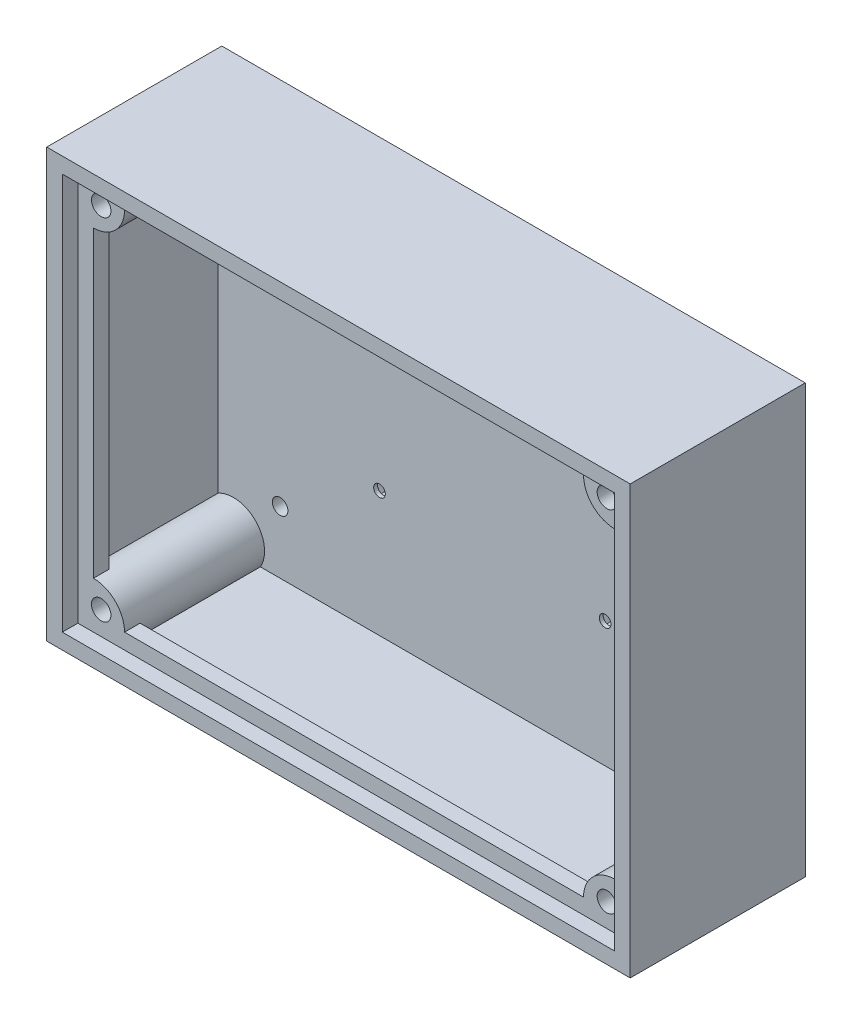
SolidWorks part; units mm, degrees
ref_plane "Front Plane" through (0, 0, 0) normal (0, 0, 1) x (1, 0, 0)
ref_plane "Top Plane" through (0, 0, 0) normal (0, 1, 0) x (1, 0, 0)
ref_plane "Right Plane" through (0, 0, 0) normal (1, 0, 0) x (0, 0, -1)
sketch "Sketch1" plane through (0, 0, 0) normal (0, 0, 1) x (1, 0, 0)
  line L1 (-102.1814, 48.3946) -> (47.8186, 48.3946)
  line L2 (-102.1814, 48.3946) -> (-102.1814, -61.6054)
  line L3 (-102.1814, -61.6054) -> (47.8186, -61.6054)
  line L4 (47.8186, 48.3946) -> (47.8186, -61.6054)
  dimension "D1" = 110
  dimension "D2" = 150
extrude "Boss-Extrude1" add sketch "Sketch1" along normal blind 5
sketch "Sketch2" plane through (0, 0, 5) normal (0, 0, 1) x (-1, 0, 0)
  line L0 (56.6312, -23.6539) -> (-1.3688, -23.6539) construction
  line L1 (-1.3688, -23.6539) -> (-1.3688, 25.3461) construction
  line L2 (-1.3688, 25.3461) -> (56.6312, 25.3461) construction
  line L3 (56.6312, 25.3461) -> (56.6312, -23.6539) construction
  line L4 (73.9008, -28.3946) -> (73.9008, 31.3544) construction
  line L5 (73.9008, 31.3544) -> (-19.5381, 31.3544) construction
  line L6 (-19.5381, 31.3544) -> (-19.5381, -28.3946) construction
  line L7 (-19.5381, -28.3946) -> (73.9008, -28.3946) construction
  line L8 (102.1814, 61.6054) -> (-47.8186, 61.6054) construction
  line L9 (0.9983, 25.3461) -> (-0.1852, 27.3961)
  line L10 (-47.8186, 61.6054) -> (-47.8186, -48.3946) construction
  line L11 (-47.8186, -48.3946) -> (102.1814, -48.3946) construction
  line L12 (-0.1852, 27.3961) -> (-2.5524, 27.3961)
  line L13 (-2.5524, 27.3961) -> (-3.7359, 25.3461)
  line L14 (-3.7359, 25.3461) -> (-2.5524, 23.2961)
  line L15 (-2.5524, 23.2961) -> (-0.1852, 23.2961)
  line L16 (-0.1852, 23.2961) -> (0.9983, 25.3461)
  line L17 (55.4476, 27.3961) -> (54.2641, 25.3461)
  line L18 (54.2641, 25.3461) -> (55.4476, 23.2961)
  line L19 (55.4476, 23.2961) -> (57.8148, 23.2961)
  line L20 (57.8148, 23.2961) -> (58.9983, 25.3461)
  line L21 (58.9983, 25.3461) -> (57.8148, 27.3961)
  line L22 (57.8148, 27.3961) -> (55.4476, 27.3961)
  line L23 (-0.1852, -21.6039) -> (-2.5524, -21.6039)
  line L24 (-2.5524, -21.6039) -> (-3.7359, -23.6539)
  line L25 (-3.7359, -23.6539) -> (-2.5524, -25.7039)
  line L26 (-2.5524, -25.7039) -> (-0.1852, -25.7039)
  line L27 (-0.1852, -25.7039) -> (0.9983, -23.6539)
  line L28 (0.9983, -23.6539) -> (-0.1852, -21.6039)
  line L29 (55.4476, -21.6039) -> (54.2641, -23.6539)
  line L30 (54.2641, -23.6539) -> (55.4476, -25.7039)
  line L31 (55.4476, -25.7039) -> (57.8148, -25.7039)
  line L32 (57.8148, -25.7039) -> (58.9983, -23.6539)
  line L33 (58.9983, -23.6539) -> (57.8148, -21.6039)
  line L34 (57.8148, -21.6039) -> (55.4476, -21.6039)
  circle A0 centre (-1.3688, 25.3461) radius 1.35
  circle A1 centre (56.6312, 25.3461) radius 1.35
  circle A2 centre (56.6312, -23.6539) radius 1.35
  circle A3 centre (-1.3688, -23.6539) radius 1.3
  circle A4 centre (-1.3688, 25.3461) radius 2.05 construction
  circle A5 centre (56.6312, 25.3461) radius 2.05 construction
  circle A6 centre (-1.3688, -23.6539) radius 2.05 construction
  circle A7 centre (56.6312, -23.6539) radius 2.05 construction
  dimension "D1" = 28.2806
  dimension "D2" = 59.7491
  dimension "D3" = 93.4389
  dimension "D4" = 58
  dimension "D5" = 49
  dimension "D6" = 4.7408
  dimension "D7" = 17.2696
  dimension "D8" = 20
  dimension "D9" = 4.1
sketch "Sketch3" plane through (0, 0, 5) normal (0, 0, 1) x (1, 0, 0)
  line L1 (43.1338, -96.4138) -> (44.7504, -93.6138)
  line L2 (44.7504, -93.6138) -> (43.1338, -90.8138)
  line L3 (43.1338, -90.8138) -> (39.9006, -90.8138)
  line L4 (39.9006, -90.8138) -> (38.284, -93.6138)
  line L5 (38.284, -93.6138) -> (39.9006, -96.4138)
  line L6 (39.9006, -96.4138) -> (43.1338, -96.4138)
  line L7 (92.1338, -96.4138) -> (93.7504, -93.6138)
  line L8 (93.7504, -93.6138) -> (92.1338, -90.8138)
  line L9 (92.1338, -90.8138) -> (88.9006, -90.8138)
  line L10 (88.9006, -90.8138) -> (87.284, -93.6138)
  line L11 (87.284, -93.6138) -> (88.9006, -96.4138)
  line L12 (88.9006, -96.4138) -> (92.1338, -96.4138)
  line L13 (43.1338, -154.4138) -> (44.7504, -151.6138)
  line L14 (44.7504, -151.6138) -> (43.1338, -148.8138)
  line L15 (43.1338, -148.8138) -> (39.9006, -148.8138)
  line L16 (39.9006, -148.8138) -> (38.284, -151.6138)
  line L17 (38.284, -151.6138) -> (39.9006, -154.4138)
  line L18 (39.9006, -154.4138) -> (43.1338, -154.4138)
  line L19 (92.1338, -154.4138) -> (93.7504, -151.6138)
  line L20 (93.7504, -151.6138) -> (92.1338, -148.8138)
  line L21 (92.1338, -148.8138) -> (88.9006, -148.8138)
  line L22 (88.9006, -148.8138) -> (87.284, -151.6138)
  line L23 (87.284, -151.6138) -> (88.9006, -154.4138)
  line L24 (88.9006, -154.4138) -> (92.1338, -154.4138)
  line L27 (41.5172, -93.6138) -> (90.5172, -93.6138)
  line L28 (41.5172, -93.6138) -> (41.5172, -151.6138)
  line L29 (41.5172, -151.6138) -> (90.5172, -151.6138)
  line L30 (90.5172, -93.6138) -> (90.5172, -151.6138)
  circle A0 centre (41.5172, -93.6138) radius 2.8 construction
  circle A1 centre (90.5172, -93.6138) radius 2.8 construction
  circle A2 centre (41.5172, -151.6138) radius 2.8 construction
  circle A3 centre (90.5172, -151.6138) radius 2.8 construction
  dimension "D1" = 58
  dimension "D2" = 49
  dimension "D5" = 5.6
sketch "Sketch4" plane through (0, 0, 5) normal (0, 0, 1) x (1, 0, 0)
  line L15 (43.8186, -57.6054) -> (43.8186, 44.3946)
  line L16 (-98.1814, -57.6054) -> (43.8186, -57.6054)
  line L17 (43.8186, 44.3946) -> (-98.1814, 44.3946)
  line L18 (-98.1814, 44.3946) -> (-98.1814, -57.6054)
  line L19 (43.8186, -57.6054) -> (43.8186, 44.3946)
  line L20 (-98.1814, -57.6054) -> (43.8186, -57.6054)
  line L21 (43.8186, 44.3946) -> (-98.1814, 44.3946)
  line L22 (-98.1814, 44.3946) -> (-98.1814, -57.6054)
  line L33 (-102.1814, -61.6054) -> (47.8186, -61.6054)
  line L34 (47.8186, -61.6054) -> (47.8186, 48.3946)
  line L35 (47.8186, 48.3946) -> (-102.1814, 48.3946)
  line L36 (-102.1814, 48.3946) -> (-102.1814, -61.6054)
  line L37 (-102.1814, -61.6054) -> (47.8186, -61.6054)
  line L38 (47.8186, -61.6054) -> (47.8186, 48.3946)
  line L39 (47.8186, 48.3946) -> (-102.1814, 48.3946)
  line L40 (-102.1814, 48.3946) -> (-102.1814, -61.6054)
  dimension "D1" = 4
  dimension "D2" = 0
extrude "Boss-Extrude2" add sketch "Sketch4" along normal blind 40
extrude "Cut-Extrude1" cut sketch "Sketch2" against normal through all contours L9 L12 L13 L14 L15 L16 | L17 L18 L19 L20 L21 L22 | L29 L30 L31 L32 L33 L34 | L23 L24 L25 L26 L27 L28
sketch "Sketch5" plane through (0, 0, 45) normal (0, 0, 1) x (1, 0, 0)
  line L10 (39.8186, 40.3946) -> (-94.1814, 40.3946)
  line L11 (-94.1814, 40.3946) -> (-94.1814, -53.6054)
  line L12 (-94.1814, -53.6054) -> (39.8186, -53.6054)
  line L13 (39.8186, -53.6054) -> (39.8186, 40.3946)
  line L14 (43.8186, 44.3946) -> (-98.1814, 44.3946)
  line L15 (43.8186, -57.6054) -> (43.8186, 44.3946)
  line L16 (-98.1814, -57.6054) -> (43.8186, -57.6054)
  line L17 (-98.1814, 44.3946) -> (-98.1814, -57.6054)
  line L18 (43.8186, 44.3946) -> (-98.1814, 44.3946)
  line L19 (43.8186, -57.6054) -> (43.8186, 44.3946)
  line L20 (-98.1814, -57.6054) -> (43.8186, -57.6054)
  line L21 (-98.1814, 44.3946) -> (-98.1814, -57.6054)
  dimension "D1" = 0
  dimension "D2" = 4
extrude "Boss-Extrude3" add sketch "Sketch5" against normal blind 8
sketch "Sketch6" plane through (0, 0, 45) normal (0, 0, 1) x (1, 0, 0)
  line L10 (39.8186, 40.3946) -> (-94.1814, 40.3946)
  line L11 (-94.1814, 40.3946) -> (-94.1814, -53.6054)
  line L12 (-94.1814, -53.6054) -> (39.8186, -53.6054)
  line L13 (39.8186, -53.6054) -> (39.8186, 40.3946)
  line L18 (43.8186, 44.3946) -> (-98.1814, 44.3946)
  line L19 (43.8186, -57.6054) -> (43.8186, 44.3946)
  line L20 (-98.1814, -57.6054) -> (43.8186, -57.6054)
  line L21 (-98.1814, 44.3946) -> (-98.1814, -57.6054)
  dimension "D2" = 4
extrude "Cut-Extrude2" cut sketch "Sketch6" against normal blind 4
sketch "Sketch7" plane through (0, 0, 41) normal (0, 0, 1) x (1, 0, 0)
  line L0 (-94.1814, -53.6054) -> (39.8186, -53.6054) construction
  circle A0 centre (-94.1814, 40.3946) radius 8
  circle A1 centre (-94.1814, -53.6054) radius 8
  circle A2 centre (39.8186, -53.6054) radius 8
  circle A3 centre (39.8186, 40.3946) radius 8
extrude "Boss-Extrude4" add sketch "Sketch7" against normal up to surface (36 mm away) up to face at (1.3688, 23.6539, 5)
sketch "Sketch8" plane through (0, 0, 41) normal (0, 0, 1) x (1, 0, 0)
  line L1 (-92.1814, 38.3946) -> (37.8186, 38.3946)
  line L2 (-92.1814, 38.3946) -> (-92.1814, -51.6054)
  line L3 (-92.1814, -51.6054) -> (37.8186, -51.6054)
  line L4 (37.8186, 38.3946) -> (37.8186, -51.6054)
  line L5 (-98.1814, 44.3946) -> (-98.1814, -57.6054) construction
  line L6 (43.8186, 44.3946) -> (-98.1814, 44.3946) construction
  line L7 (-98.1814, -57.6054) -> (43.8186, -57.6054) construction
  line L8 (43.8186, -57.6054) -> (43.8186, 44.3946) construction
  circle A0 centre (-92.1814, 38.3946) radius 2.5
  circle A1 centre (37.8186, 38.3946) radius 2.5
  circle A2 centre (-92.1814, -51.6054) radius 2.5
  circle A3 centre (37.8186, -51.6054) radius 2.5
  dimension "D1" = 5
  dimension "D2" = 6
  dimension "D3" = 6
  dimension "D4" = 6
  dimension "D5" = 6
extrude "Cut-Extrude3" cut sketch "Sketch8" against normal up to surface (36 mm away) contours L1 A0 L2 | L2 A0 L1 | L1 A1 L4 | L4 A1 L1 | L4 A3 L3 | L3 A3 L4 | L2 A2 L3 | L3 A2 L2 up to face at (-27.1814, -6.6054, 5)
sketch "Sketch9" plane through (0, 0, 0) normal (0, 0, -1) x (-1, 0, 0)
  line L0 (-47.8186, -61.6054) -> (-47.8186, 48.3946) construction
  line L1 (-27.8186, 28.3946) -> (82.1814, 28.3946)
  line L2 (-27.8186, 28.3946) -> (-27.8186, -41.6054)
  line L3 (-27.8186, -41.6054) -> (82.1814, -41.6054)
  line L4 (82.1814, 28.3946) -> (82.1814, -41.6054)
  line L5 (102.1814, -61.6054) -> (-47.8186, -61.6054) construction
  line L6 (102.1814, 48.3946) -> (102.1814, -61.6054) construction
  line L7 (-47.8186, 48.3946) -> (102.1814, 48.3946) construction
  circle A0 centre (-27.8186, 28.3946) radius 2
  circle A1 centre (82.1814, 28.3946) radius 2
  circle A2 centre (-27.8186, -41.6054) radius 2
  circle A3 centre (82.1814, -41.6054) radius 2
  dimension "D5" = 4
  dimension "D1" = 20
  dimension "D2" = 20
  dimension "D3" = 20
  dimension "D4" = 20
extrude "Cut-Extrude4" cut sketch "Sketch9" against normal through all contours L1 A0 L2 | L2 A0 L1 | L2 A2 L3 | L3 A2 L2 | L3 A3 L4 | L4 A3 L3 | L1 A1 L4 | L4 A1 L1
sketch "Sketch10" plane through (0, 0, 5) normal (0, 0, 1) x (1, 0, 0)
  line L0 (-58.9983, 23.6539) -> (-54.2641, 23.6539) construction
  line L1 (-54.2641, 23.6539) -> (3.7359, 23.6539) construction
  line L2 (3.7359, -25.3461) -> (-0.9983, -25.3461) construction
  line L3 (-0.9983, 23.6539) -> (3.7359, 23.6539)
  line L4 (-55.4476, 25.7039) -> (-57.8148, 25.7039)
  line L5 (-57.8148, 25.7039) -> (-58.9983, 23.6539)
  line L6 (-58.9983, 23.6539) -> (-57.8148, 21.6039)
  line L7 (-57.8148, 21.6039) -> (-55.4476, 21.6039)
  line L8 (-55.4476, 21.6039) -> (-54.2641, 23.6539)
  line L9 (-54.2641, 23.6539) -> (-55.4476, 25.7039)
  line L10 (-54.2641, -25.3461) -> (-58.9983, -25.3461) construction
  line L11 (2.5524, 25.7039) -> (0.1852, 25.7039)
  line L12 (0.1852, 25.7039) -> (-0.9983, 23.6539)
  line L13 (-0.9983, 23.6539) -> (0.1852, 21.6039)
  line L14 (0.1852, 21.6039) -> (2.5524, 21.6039)
  line L15 (2.5524, 21.6039) -> (3.7359, 23.6539)
  line L16 (3.7359, 23.6539) -> (2.5524, 25.7039)
  line L18 (-55.4476, -23.2961) -> (-57.8148, -23.2961)
  line L19 (-57.8148, -23.2961) -> (-58.9983, -25.3461)
  line L20 (-58.9983, -25.3461) -> (-57.8148, -27.3961)
  line L21 (-57.8148, -27.3961) -> (-55.4476, -27.3961)
  line L22 (-55.4476, -27.3961) -> (-54.2641, -25.3461)
  line L23 (-54.2641, -25.3461) -> (-55.4476, -23.2961)
  line L24 (2.5524, -23.2961) -> (0.1852, -23.2961)
  line L25 (0.1852, -23.2961) -> (-0.9983, -25.3461)
  line L26 (-0.9983, -25.3461) -> (0.1852, -27.3961)
  line L27 (0.1852, -27.3961) -> (2.5524, -27.3961)
  line L28 (2.5524, -27.3961) -> (3.7359, -25.3461)
  line L29 (3.7359, -25.3461) -> (2.5524, -23.2961)
  circle A0 centre (-56.6312, 23.6539) radius 2.05 construction
  circle A1 centre (1.3688, 23.6539) radius 2.05 construction
  circle A2 centre (-56.6312, -25.3461) radius 2.05 construction
  circle A3 centre (1.3688, -25.3461) radius 2.05 construction
  circle A4 centre (1.3688, -25.3461) radius 1.5
  circle A5 centre (1.3688, 23.6539) radius 1.5
  circle A6 centre (-56.6312, 23.6539) radius 1.5
  circle A7 centre (-56.6312, -25.3461) radius 1.5
  line M22 (-0.9983, 23.6539) -> (0.1852, 25.7039)
  line M23 (0.1852, 25.7039) -> (2.5524, 25.7039)
  line M24 (2.5524, 25.7039) -> (3.7359, 23.6539)
  line M27 (-55.4476, 21.6039) -> (-57.8148, 21.6039)
  line M28 (-57.8148, 21.6039) -> (-58.9983, 23.6539)
  line M29 (-58.9983, 23.6539) -> (-57.8148, 25.7039)
  line M30 (-57.8148, 25.7039) -> (-55.4476, 25.7039)
  line M31 (-55.4476, 25.7039) -> (-54.2641, 23.6539)
  line M32 (-54.2641, 23.6539) -> (-55.4476, 21.6039)
  line M33 (-55.4476, -27.3961) -> (-57.8148, -27.3961)
  line M34 (-57.8148, -27.3961) -> (-58.9983, -25.3461)
  line M35 (-58.9983, -25.3461) -> (-57.8148, -23.2961)
  line M36 (-57.8148, -23.2961) -> (-55.4476, -23.2961)
  line M37 (-55.4476, -23.2961) -> (-54.2641, -25.3461)
  line M38 (-54.2641, -25.3461) -> (-55.4476, -27.3961)
  line M39 (-0.9983, -25.3461) -> (0.1852, -23.2961)
  line M40 (0.1852, -23.2961) -> (2.5524, -23.2961)
  line M41 (2.5524, -23.2961) -> (3.7359, -25.3461)
  line M42 (3.7359, -25.3461) -> (2.5524, -27.3961)
  line M43 (2.5524, -27.3961) -> (0.1852, -27.3961)
  line M44 (0.1852, -27.3961) -> (-0.9983, -25.3461)
  dimension "D1" = 3
extrude "Boss-Extrude5" add sketch "Sketch10" against normal blind 1 contours A6 M27 M32 M31 M30 M29 M28 | A5 L3 M24 M23 M22 | A4 M39 M44 M43 M42 M41 M40 | A7 M33 M38 M37 M36 M35 M34
